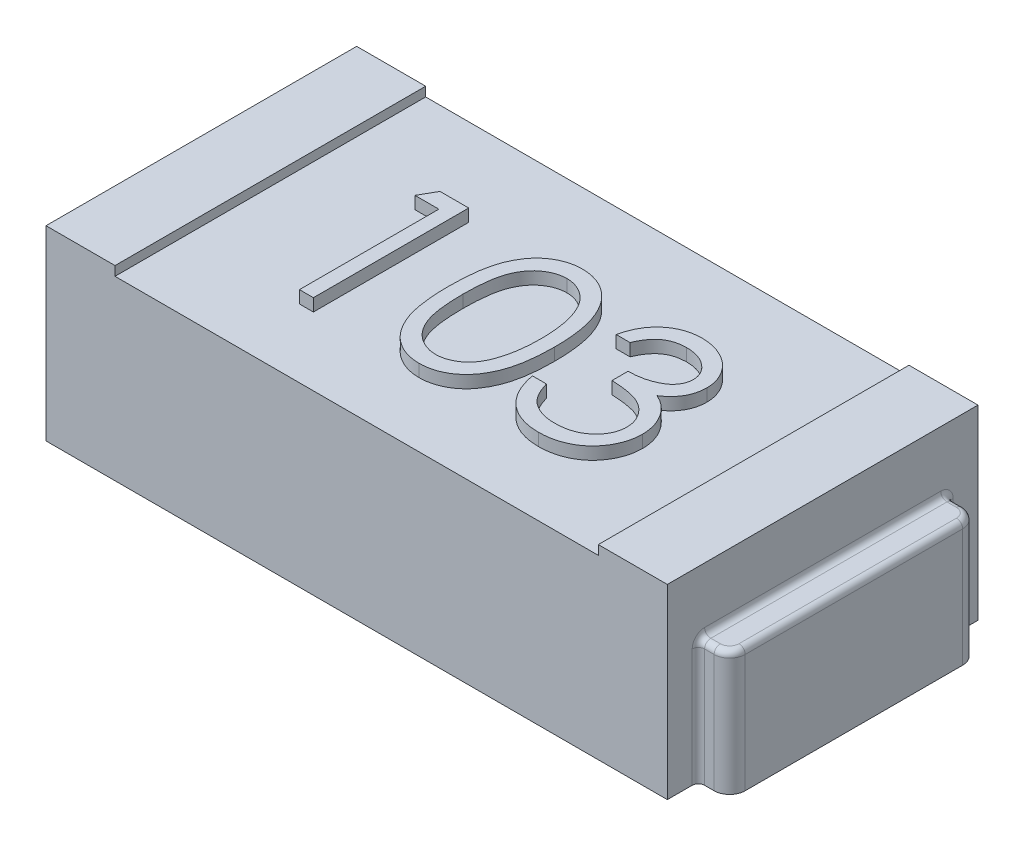
SolidWorks part; units mm, degrees
ref_plane "Plan de face" through (0, 0, 0) normal (0, 0, 1) x (1, 0, 0)
ref_plane "Plan de dessus" through (0, 0, 0) normal (0, 1, 0) x (1, 0, 0)
ref_plane "Plan de droite" through (0, 0, 0) normal (1, 0, 0) x (0, 0, -1)
sketch "Esquisse1" plane through (0, 0, 0) normal (0, 1, 0) x (1, 0, 0)
  line L1 (1, -0.5) -> (-1, -0.5)
  line L2 (1, -0.5) -> (1, 0.5)
  line L3 (1, 0.5) -> (-1, 0.5)
  line L4 (-1, -0.5) -> (-1, 0.5)
  line L5 (1, -0.5) -> (-1, 0.5) construction
  line L6 (1, 0.5) -> (-1, -0.5) construction
  point P0 (0, 0)
  dimension "D1" = 2
  dimension "D2" = 1
extrude "Boss.-Extru.1" add sketch "Esquisse1" along normal blind 0.6
sketch "Esquisse2" plane through (0, 0.6, 0) normal (0, 1, 0) x (1, 0, 0)
  line L0 (1, 0.5) -> (-1, 0.5) construction
  line L1 (0.7778, -0.5) -> (-0.7778, -0.5)
  line L2 (0.7778, -0.5) -> (0.7778, 0.5)
  line L3 (0.7778, 0.5) -> (-0.7778, 0.5)
  line L4 (-0.7778, -0.5) -> (-0.7778, 0.5)
  line L5 (0.7778, -0.5) -> (-0.7778, 0.5) construction
  line L6 (0.7778, 0.5) -> (-0.7778, -0.5) construction
  point P0 (0, 0)
extrude "Enlèv. mat.-Extru.1" cut sketch "Esquisse2" against normal blind 0.03
sketch "Esquisse3" plane through (0, 0, 0) normal (0, 1, 0) x (1, 0, 0)
  line L1 (1, 0.4) -> (1.0506, 0.4)
  line L2 (1, 0.4) -> (1, -0.4)
  line L3 (1, -0.4) -> (1.0506, -0.4)
  line L4 (1.1006, 0.35) -> (1.1006, -0.35)
  line L8 (1, -0.5) -> (1, 0.5) construction
  arc A0 (1.0506, -0.4) -> (1.1006, -0.35) centre (1.0506, -0.35) ccw
  arc A1 (1.0506, 0.4) -> (1.1006, 0.35) centre (1.0506, 0.35) cw
  dimension "D1" = 0.05
  dimension "D2" = 0.8
  dimension "D3" = 0.1006
extrude "Boss.-Extru.2" add sketch "Esquisse3" along normal blind 0.4
fillet "Congé1" radius 0.02 8 edges at (1, 0.2, -0.4) (1, 0.2, 0.4) (1.0253, 0.4, -0.4) (1.0859, 0.4, -0.3854) (1.1006, 0.4, 0) (1.0859, 0.4, 0.3854) (1.0253, 0.4, 0.4) (1, 0.4, 0)
mirror "Symétrie2" about plane through (0, 0, 0) normal (1, 0, 0) of "Congé1", "Boss.-Extru.2"
sketch "Esquisse4" plane through (0, 0.57, 0) normal (0, 1, 0) x (1, 0, 0)
  line L0 (0.7576, -0.2803) -> (-0.7576, -0.2803) construction
  text T0 "103\r\n" font "Century Gothic" height 0.5
  point P3 (0, -0.2803)
extrude "Boss.-Extru.3" add sketch "Esquisse4" along normal blind 0.04
